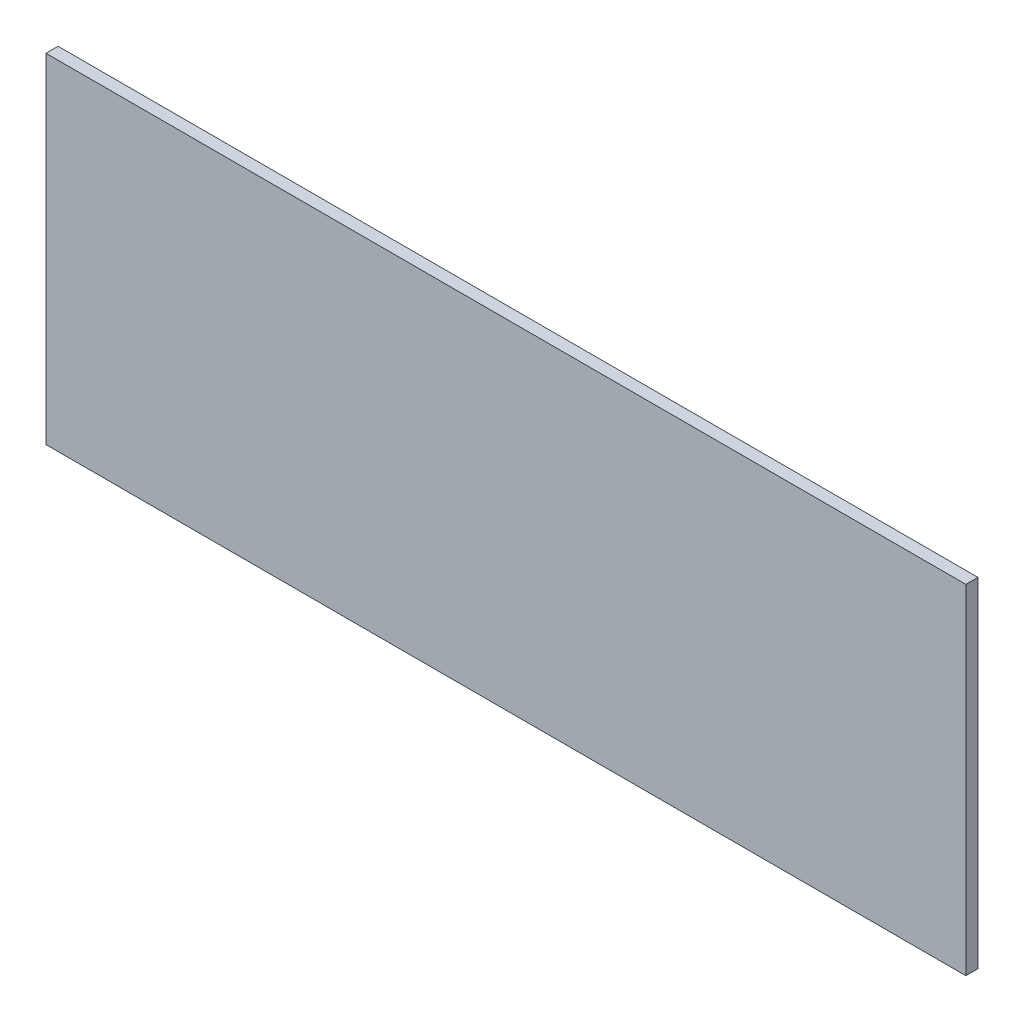
SolidWorks part; units mm, degrees
ref_plane "Front Plane" through (0, 0, 0) normal (0, 0, 1) x (1, 0, 0)
ref_plane "Top Plane" through (0, 0, 0) normal (0, 1, 0) x (1, 0, 0)
ref_plane "Right Plane" through (0, 0, 0) normal (1, 0, 0) x (0, 0, -1)
sketch "Sketch1" plane through (0, 0, 0) normal (0, 0, 1) x (1, 0, 0)
  line L1 (0, 0) -> (482.6, 0)
  line L2 (0, 0) -> (0, 177.8)
  line L3 (0, 177.8) -> (482.6, 177.8)
  line L4 (482.6, 0) -> (482.6, 177.8)
  dimension "D1" = 177.8
  dimension "D2" = 482.6
extrude "Boss-Extrude1" add sketch "Sketch1" along normal blind 6.35
